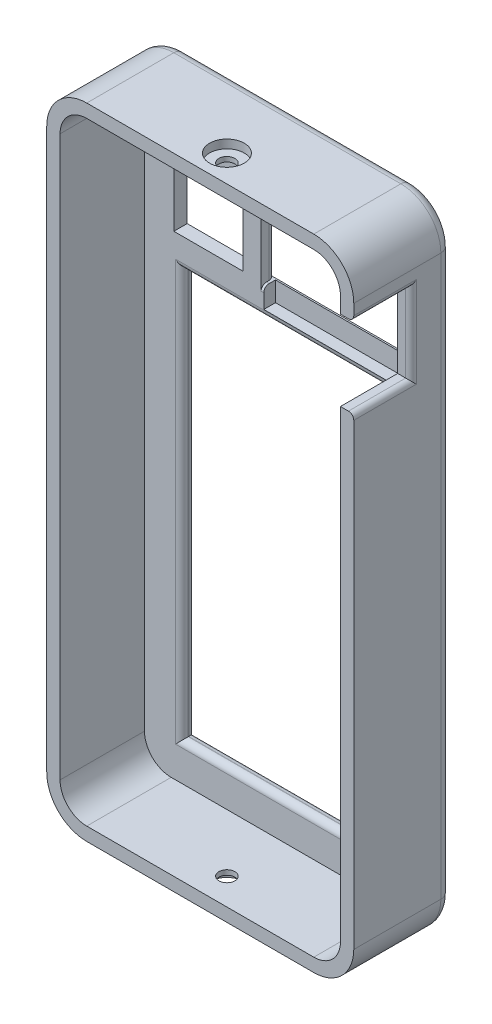
SolidWorks part; units mm, degrees
ref_plane "Front Plane" through (0, 0, 0) normal (0, 0, 1) x (1, 0, 0)
ref_plane "Top Plane" through (0, 0, 0) normal (0, 1, 0) x (1, 0, 0)
ref_plane "Right Plane" through (0, 0, 0) normal (1, 0, 0) x (0, 0, -1)
sketch "Sketch1" plane through (0, 0, 0) normal (0, 0, 1) x (1, 0, 0)
  line L24 (15.6157, 54.5139) -> (58.1937, 54.5139)
  line L25 (65.6937, 62.0139) -> (65.6937, 166.9489)
  line L26 (8.1157, 166.9489) -> (8.1157, 62.0139)
  line L27 (58.1937, 174.4489) -> (15.6157, 174.4489)
  line L28 (15.6157, 54.5139) -> (58.1937, 54.5139)
  line L29 (65.6937, 62.0139) -> (65.6937, 166.9489)
  line L30 (8.1157, 166.9489) -> (8.1157, 62.0139)
  line L31 (58.1937, 174.4489) -> (15.6157, 174.4489)
  arc A20 (8.1157, 62.0139) -> (15.6157, 54.5139) centre (15.6157, 62.0139) ccw
  arc A21 (58.1937, 54.5139) -> (65.6937, 62.0139) centre (58.1937, 62.0139) ccw
  arc A22 (65.6937, 166.9489) -> (58.1937, 174.4489) centre (58.1937, 166.9489) ccw
  arc A23 (15.6157, 174.4489) -> (8.1157, 166.9489) centre (15.6157, 166.9489) ccw
  arc A24 (8.1157, 62.0139) -> (15.6157, 54.5139) centre (15.6157, 62.0139) ccw
  arc A25 (58.1937, 54.5139) -> (65.6937, 62.0139) centre (58.1937, 62.0139) ccw
  arc A26 (65.6937, 166.9489) -> (58.1937, 174.4489) centre (58.1937, 166.9489) ccw
  arc A27 (15.6157, 174.4489) -> (8.1157, 166.9489) centre (15.6157, 166.9489) ccw
  dimension "D1" = 2.5
extrude "Boss-Extrude1" add sketch "Sketch1" against normal offset from surface (18.3324 mm away) 8
shell "Shell2" thickness 2.5
sketch "Sketch2" plane through (0, 0, -18.3324) normal (0, 0, -1) x (-1, 0, 0)
  line L0 (-15.6157, 174.4489) -> (-58.1937, 174.4489) construction
  line L1 (-33.4793, 169.0868) -> (-39.6793, 169.0868) construction
  line L2 (-32.4793, 145.3868) -> (-58.8793, 145.3868)
  line L3 (-32.4793, 145.3868) -> (-32.4793, 164.4868)
  line L4 (-32.4793, 164.4868) -> (-58.8793, 164.4868)
  line L5 (-58.8793, 145.3868) -> (-58.8793, 164.4868)
  line L6 (-32.9793, 142.1868) -> (-32.9793, 168.5868) construction
  line L7 (-61.3793, 168.5868) -> (-61.3793, 142.1868) construction
  line L8 (-60.8793, 141.6868) -> (-33.4793, 141.6868) construction
  line L9 (-29.1157, 158.9489) -> (-16.1157, 158.9489)
  line L14 (-29.1157, 158.9489) -> (-29.1157, 145.9489)
  line L15 (-29.1157, 145.9489) -> (-16.1157, 145.9489)
  line L16 (-16.1157, 158.9489) -> (-16.1157, 145.9489)
  line L17 (-8.1157, 62.0139) -> (-8.1157, 166.9489) construction
  line L18 (-56.1937, 140.3868) -> (-17.6157, 140.3868)
  line L19 (-56.1937, 140.3868) -> (-56.1937, 64.0139)
  line L20 (-56.1937, 64.0139) -> (-17.6157, 64.0139)
  line L21 (-17.6157, 140.3868) -> (-17.6157, 64.0139)
  line L22 (-65.6937, 166.9489) -> (-65.6937, 62.0139) construction
  line L23 (-58.1937, 54.5139) -> (-15.6157, 54.5139) construction
  dimension "D1" = 13
  dimension "D2" = 4.6
  dimension "D3" = 0.5
  dimension "D4" = 2.5
  dimension "D5" = 3.7
  dimension "D6" = 9.5
  dimension "D7" = 9.5
  dimension "D8" = 5
  dimension "D9" = 9.5
  dimension "D10" = 13
  dimension "D11" = 15.5
  dimension "D12" = 8
extrude "Cut-Extrude1" cut sketch "Sketch2" against normal blind 4
fillet "Fillet1" radius 2 8 edges at (10.3124, 172.2522, -18.3324) (8.1157, 114.4814, -18.3324) (10.3124, 56.7106, -18.3324) (36.9047, 54.5139, -18.3324) (63.497, 56.7106, -18.3324) (65.6937, 114.4814, -18.3324) (63.497, 172.2522, -18.3324) (36.9047, 174.4489, -18.3324)
fillet "Fillet2" radius 1.2 8 edges at (36.9047, 140.3868, -18.3324) (36.9047, 64.0139, -15.8324) (17.6157, 102.2003, -15.8324) (36.9047, 64.0139, -18.3324) (17.6157, 102.2003, -18.3324) (36.9047, 140.3868, -15.8324) (56.1937, 102.2003, -15.8324) (56.1937, 102.2003, -18.3324)
fillet "Fillet4" radius 1 5 edges at (45.6793, 164.4868, -15.8324) (45.6793, 145.3868, -15.8324) (58.8793, 154.9368, -18.3324) (32.4793, 154.9368, -18.3324) (45.6793, 164.4868, -18.3324)
sketch "Sketch3" plane through (65.6937, 0, 0) normal (1, 0, 0) x (0, 0, -1)
  line L0 (0, 62.0139) -> (0, 166.9489) construction
  line L1 (0, 163.9489) -> (10.7324, 163.9489)
  line L2 (0, 163.9489) -> (0, 148.9489)
  line L3 (0, 148.9489) -> (10.7324, 148.9489)
  line L4 (10.7324, 163.9489) -> (10.7324, 148.9489)
  line L5 (16.3324, 166.9489) -> (0, 166.9489) construction
  line L6 (18.3324, 166.9489) -> (18.3324, 62.0139) construction
  point P8 (8.1662, 166.9489)
  dimension "D1" = 15
  dimension "D2" = 3
  dimension "D3" = 7.6
extrude "Cut-Extrude2" cut sketch "Sketch3" against normal up to next
fillet "Fillet5" radius 1 3 edges at (65.6937, 156.4489, -10.7324) (65.6937, 163.9489, -5.3662) (65.6937, 148.9489, -5.3662)
sketch "Sketch6" plane through (0, 0, -15.8324) normal (0, 0, 1) x (1, 0, 0)
  line L0 (32.9793, 142.1868) -> (32.9793, 168.5868) construction
  line L1 (59.4533, 169.0868) -> (32.9793, 169.0868)
  line L2 (59.4533, 169.0868) -> (59.4533, 141.6868)
  line L3 (59.4533, 141.6868) -> (32.9793, 141.6868)
  line L4 (32.9793, 169.0868) -> (32.9793, 141.6868)
  line L5 (54.6793, 169.0868) -> (60.8793, 169.0868) construction
  line L6 (60.8793, 141.6868) -> (33.4793, 141.6868) construction
  dimension "D1" = 0
  dimension "D2" = 0
  dimension "D3" = 0
  dimension "D4" = 0
extrude "Cut-Extrude5" cut sketch "Sketch6" against normal blind 2.2
sketch "Sketch7" plane through (0, 174.4489, 0) normal (0, 1, 0) x (1, 0, 0)
  circle A0 centre (36.9047, 5) radius 3.25
  dimension "D1" = 6.5
extrude "Cut-Extrude6" cut sketch "Sketch7" against normal blind 1.6
sketch "Sketch8" plane through (0, 54.5139, 0) normal (0, -1, 0) x (1, 0, 0)
  circle A0 centre (36.9047, -5) radius 3.25
  dimension "D1" = 6.5
extrude "Cut-Extrude7" cut sketch "Sketch8" against normal blind 1.6
sketch "Sketch9" plane through (0, 56.1139, 0) normal (0, -1, 0) x (1, 0, 0)
  circle A0 centre (36.9047, -5) radius 1.5
  dimension "D1" = 3
extrude "Cut-Extrude8" cut sketch "Sketch9" against normal blind 5
sketch "Sketch10" plane through (0, 172.8489, 0) normal (0, 1, 0) x (1, 0, 0)
  circle A0 centre (36.9047, 5) radius 1.5
  dimension "D1" = 3
extrude "Cut-Extrude9" cut sketch "Sketch10" against normal blind 5
